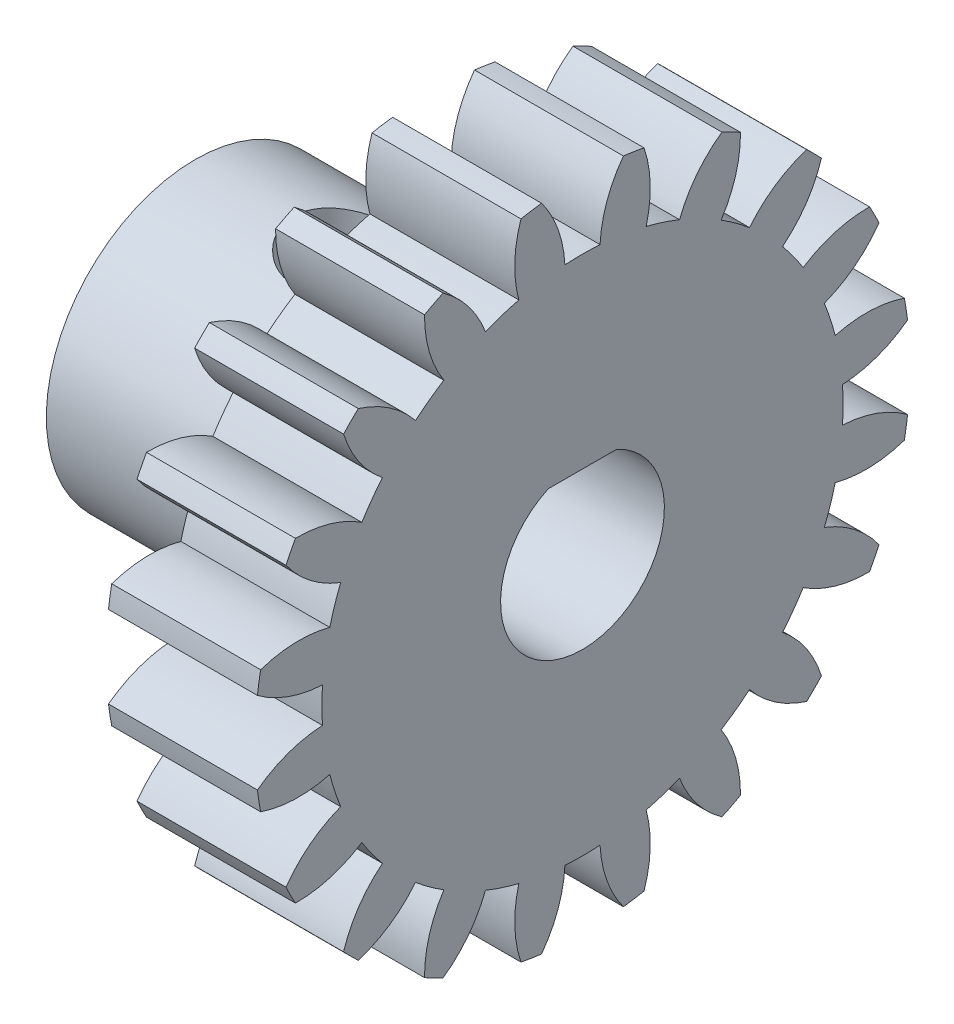
SolidWorks part; units mm, degrees
ref_plane "Plane1" through (0, 0, 0) normal (0, 0, 1) x (1, 0, 0)
ref_plane "Plane2" through (0, 0, 0) normal (0, 1, 0) x (1, 0, 0)
ref_plane "Plane3" through (0, 0, 0) normal (1, 0, 0) x (0, 0, -1)
sketch "HoldingSke" plane through (0, 0, 0) normal (0, 1, 0) x (1, 0, 0)
  line L0 (0, 0) -> (0.9397, -0.342)
  line L1 (-15, 0) -> (100, 0) construction
  line L2 (0, 0) -> (-2.1039, 2.3779)
  line L3 (0, 0) -> (-11.863, 4.5341)
  line L4 (0, 0) -> (8.1152, 2.9537)
  line L5 (0, 0) -> (-14.0543, -5.2418)
  line L6 (0, 0) -> (-4.1448, -2.7965)
  line L7 (-2.1039, 2.3779) -> (1.1249, 17.0263)
  line L8 (-76.2, 54.61) -> (-75.2, 54.61)
  line L9 (-67.7845, 28.3722) -> (-49.3413, 33.142)
  line L10 (-76.2, 71.12) -> (104.1128, 71.12)
  line L11 (0, 0) -> (-5, 0)
  line L12 (-76.2, 101.6) -> (-76.162, 101.6)
  line L13 (24.9733, 27.94) -> (52.9518, 28.4284)
  line L14 (24.9733, 27.94) -> (24.9743, 27.94)
  line L15 (24.9733, 27.94) -> (100.4006, 29.5858)
  line L16 (-63.627, -1) -> (-12.827, -1)
  circle A0 centre (0, 0) radius 3
  circle A1 centre (0, 0) radius 5
  circle A2 centre (0, 0) radius 5
  circle A3 centre (0, 0) radius 3
  dimension "MHD" = 10
  dimension "Hub_dia" = 10
  dimension "Bore" = 6
  dimension "MBD" = 6
  dimension "Num_teeth" = 20
  dimension "Pitch" = 1
  dimension "Overall_len" = 15
  dimension "Show_teeth" = 20
  dimension "Thickness" = 5
  dimension "OAL" = 15.0001
  dimension "T_dim" = 1
  dimension "Ap" = 14.5
  dimension "H" = 19.05
  dimension "Pitch_radius" = 180.3128
  dimension "Width" = 5
  dimension "Backlash" = 0.038
  dimension "Addendum_fac" = 1
  dimension "Dedendum_fac" = 1.25
  dimension "Clearance_fac" = 0.25
  dimension "Dedendum_add" = 0.001
  dimension "Module" = 1
sketch "BasProSke" plane through (0, 0, 0) normal (0, 1, 0) x (1, 0, 0)
  line L0 (-10, 0) -> (60, 0) construction
  line L1 (0, 0) -> (0, 11)
  line L2 (0, 0) -> (5, 0)
  line L3 (5, 0) -> (5, 11)
  line L4 (5, 11) -> (0, 11)
  dimension "Thickness" = 5
  dimension "Diameter" = 22
revolve "Base-Revolve" add sketch "BasProSke" angle 360 about L0
sketch "TooCutSke" plane through (0, 0, 0) normal (1, 0, 0) x (0, 0, -1)
  line L1 (0, 0) -> (0, 107) construction
  line L2 (0, 0) -> (-0.8511, 9.9637) construction
  line L3 (0, 0) -> (-3.1206, 19.7028) construction
  line L4 (-0.8511, 9.9637) -> (-1.5603, 9.8514) construction
  arc A0 (0.5894, 8.7291) -> (-0.5894, 8.7291) centre (0, 0) ccw
  arc A1 (1.3917, 10.9372) -> (-1.3917, 10.9372) centre (0, 0) ccw
  circle A2 centre (0, 0) radius 10 construction
  circle A3 centre (0, 0) radius 9.6815 construction
  arc A4 (-0.5894, 8.7291) -> (-1.3917, 10.9372) centre (-4.5843, 8.5273) ccw
  arc A5 (1.3917, 10.9372) -> (0.5894, 8.7291) centre (4.5843, 8.5273) ccw
  dimension "Root_dia" = 17.498
  dimension "Overcut_dia" = 22.0508
  dimension "Pitch_dia" = 20
  dimension "Base_dia" = 19.363
  dimension "Flank_rad" = 4
  dimension "Half_ang" = 9
  dimension "Half_CT" = 0.7181
extrude "ToothCut" cut sketch "TooCutSke" along normal through all
fillet "Breaks" [suppressed] radius 0.02
fillet "RootFillets" [suppressed] radius 0.251
pattern_circular "TeethCuts" count 20 every 18 about axis through (-10, 0, 0) along (1, 0, 0) of "ToothCut", "RootFillets", "Breaks"
sketch "HubNeaOneSke" plane through (0, 0, 0) normal (-1, 0, 0) x (0, 0, 1)
  circle A0 centre (0, 0) radius 5
  dimension "Diameter" = 10
extrude "HubNearOne" add sketch "HubNeaOneSke" along normal blind 10.0001
sketch "HubNeaBotSke" plane through (0, 0, 0) normal (-1, 0, 0) x (0, 0, 1)
  circle A0 centre (0, 0) radius 5
  dimension "Diameter" = 10
extrude "HubNearBoth" [suppressed] add sketch "HubNeaBotSke" along normal blind 5
ref_plane "FarPln" through (5, 0, 0) normal (1, 0, 0) x (0, 0, -1)
sketch "HubFarSke" plane through (5, 0, 0) normal (1, 0, 0) x (0, 0, -1)
  circle A0 centre (0, 0) radius 5
  dimension "Diameter" = 10
extrude "HubFar" [suppressed] add sketch "HubFarSke" along normal blind 5
sketch "BorSke" plane through (0, 0, 0) normal (1, 0, 0) x (0, 0, -1)
  circle A0 centre (0, 0) radius 3
  dimension "Diameter" = 6
extrude "Bore" cut sketch "BorSke" along normal mid plane 30.0001
sketch "KeySke" plane through (0, 0, 0) normal (1, 0, 0) x (0, 0, -1)
  line L0 (-1, 0) -> (-1, 4)
  line L1 (-1, 4) -> (1, 4)
  line L2 (1, 4) -> (1, 0)
  line L3 (0, 0) -> (0, 34) construction
  line L4 (-1, 0) -> (1, 0)
  dimension "Offset" = 4
  dimension "Width" = 2
extrude "Keyway" [suppressed] cut sketch "KeySke" along normal mid plane 30.0001
pattern_circular "Keyway2" [suppressed] count 2 every 90 about axis through (-10, 0, 0) along (1, 0, 0)
sketch "Sketch2" plane through (0, 0, 0) normal (1, 0, 0) x (0, 0, -1)
  line L0 (-1.65, 2.2) -> (1.65, 2.2)
  circle A0 centre (0, 0) radius 3
  arc A2 (-1.65, 2.2) -> (1.65, 2.2) centre (0, 0) ccw
  dimension "D1" = 2.75
  dimension "D3" = 6
  dimension "D2" = 2.2
extrude "Boss-Extrude1" add sketch "Sketch2" along normal up to surface (15.0001 mm away) from surface at -10.0001 contours L0 A0 up to face at (5, 0, 3) starting at face at (-10.0001, 0, 3)
sketch "Sketch3" plane through (0, 0, 0) normal (0, 1, 0) x (1, 0, 0)
  line L0 (-10.0001, 5) -> (-10.0001, -5) construction
  line L2 (0, 0) -> (-10.0001, 0) construction
  line L3 (0, 5) -> (0, -5) construction
  circle A0 centre (-3.0001, 0) radius 1.7
  dimension "D1" = 3.4
  dimension "D2" = 7
extrude "Cut-Extrude1" cut sketch "Sketch3" along normal blind 10
sketch "Sketch4" plane through (0, 0, 0) normal (0, 0, 1) x (1, 0, 0)
  line L0 (-10.0001, 5) -> (-10.0001, -5) construction
  line L1 (-10.0001, 10.1008) -> (-8.0001, 10.1008)
  line L2 (-10.0001, 10.1008) -> (-10.0001, -10.1008)
  line L3 (-10.0001, -10.1008) -> (-8.0001, -10.1008)
  line L4 (-8.0001, 10.1008) -> (-8.0001, -10.1008)
  line L5 (-10.0001, 10.1008) -> (-8.0001, -10.1008) construction
  line L6 (-10.0001, -10.1008) -> (-8.0001, 10.1008) construction
  point P0 (-9.0001, 0)
  dimension "D1" = 2
  dimension "D2" = 2
extrude "Cut-Extrude2" cut sketch "Sketch4" against normal through all both and the other way through all
sketch "Sketch5" plane through (-8.0001, 0, 0) normal (-1, 0, 0) x (0, 0, 1)
  line L0 (0, 2.75) -> (0, 2.5)
  line L1 (-1.1456, 2.5) -> (1.1456, 2.5)
  circle A0 centre (0, 0) radius 2.75
  point P10 (0, 2.5)
  line M2 (-1.65, 2.2) -> (1.65, 2.2)
  arc M3 (1.65, 2.2) -> (-1.65, 2.2) centre (0, 0) cw
  dimension "D1" = 5.5
  dimension "D2" = 90
extrude "Cut-Extrude3" cut sketch "Sketch5" against normal blind 31 contours L1 A0 M3 M2
equation "' \"Module@HoldingSke\" = 6.35"
equation "' \"Num_teeth@HoldingSke\" = 12"
equation "' \"Ap@HoldingSke\" =  20"
equation "' \"Ap@HoldingSke\" = 20"
equation "' \"Width@HoldingSke\" = 0.5 * 25.4"
equation "' \"Hub_dia@HoldingSke\"= 1 * 25.4"
equation "' \"Hub_dia@HoldingSke\" = 1 * 25.4"
equation "' \"Overall_len@HoldingSke\" = 1.0 * 25.4"
equation "' \"Bore@HoldingSke\" = 0.75 * 25.4"
equation "' \"T_dim@HoldingSke\" = 0.1 * 25.4"
equation "' \"Width@KeySke\" = 0.25 * 25.4"
equation "' \"Show_teeth@HoldingSke\" = 13"
equation "' \"Backlash@HoldingSke\" = 0.009 * 25.4"
equation "' \"Addendum_fac@HoldingSke\" = 1.0"
equation "' \"Dedendum_fac@HoldingSke\" = 1.25"
equation "' \"Dedendum_add@HoldingSke\" = 0.00005 * 25.4"
equation "' \"Clearance_fac@HoldingSke\" = 0.25"
equation "\"Pitch@HoldingSke\" = 1 / \"Module@HoldingSke\""
equation "\"Overcut_dia@TooCutSke\" = (\"Num_teeth@HoldingSke\" + 2 * \"Addendum_fac@HoldingSke\") / \"Pitch@HoldingSke\" + 0.002 * 25.4"
equation "\"Pitch_dia@TooCutSke\" = \"Num_teeth@HoldingSke\" / \"Pitch@HoldingSke\""
equation "\"Base_dia@TooCutSke\" = \"Num_teeth@HoldingSke\" / \"Pitch@HoldingSke\" * cos((\"Ap@HoldingSke\"  * 3.14159265 / 180))"
equation "\"Root_dia@TooCutSke\" = (\"Num_teeth@HoldingSke\" + 2) / \"Pitch@HoldingSke\" - 2 * (\"Addendum_fac@HoldingSke\" + \"Dedendum_fac@HoldingSke\") / \"Pitch@HoldingSke\" - \"Dedendum_add@HoldingSke\" * 2"
equation "\"Half_ang@TooCutSke\" = 180 / \"Num_teeth@HoldingSke\""
equation "\"Half_CT@TooCutSke\" = \"Num_teeth@HoldingSke\" / \"Pitch@HoldingSke\" * sin((3.14159265 / 2 / \"Num_teeth@HoldingSke\")) / 2 - 7 * \"Backlash@HoldingSke\" / 4"
equation "\"Flank_rad@TooCutSke\" = \"Num_teeth@HoldingSke\" / \"Pitch@HoldingSke\" / 5"
equation "\"Radius@RootFillets\" = \"Clearance_fac@HoldingSke\" / \"Pitch@HoldingSke\" + \"Dedendum_add@HoldingSke\""
equation "\"Break_rad@Breaks\" = 0.02 / \"Pitch@HoldingSke\""
equation "\"Thickness@HoldingSke\" = \"Width@HoldingSke\""
equation "\"OAL@HoldingSke\" = \"Thickness@HoldingSke\""
equation "\"MHD@HoldingSke\" = (\"Num_teeth@HoldingSke\" + 2) / \"Pitch@HoldingSke\" - 2 * (\"Addendum_fac@HoldingSke\" + \"Dedendum_fac@HoldingSke\")  / \"Pitch@HoldingSke\" - \"Dedendum_add@HoldingSke\" * 2"
equation "\"MBD@HoldingSke\" = (\"Num_teeth@HoldingSke\" + 2) / \"Pitch@HoldingSke\" - 2 * (\"Addendum_fac@HoldingSke\" + \"Dedendum_fac@HoldingSke\")  / \"Pitch@HoldingSke\" - \"Dedendum_add@HoldingSke\" * 2 - 0.002 * 25.4"
equation "\"MHD@HoldingSke\" = ((sgn( \"MHD@HoldingSke\" - \"Hub_dia@HoldingSke\" )-1)*( \"MHD@HoldingSke\" - \"Hub_dia@HoldingSke\" ))/-2+ \"Hub_dia@HoldingSke\""
equation "\"MBD@HoldingSke\" = ((sgn( \"MBD@HoldingSke\" - \"Bore@HoldingSke\" )-1)*( \"MBD@HoldingSke\" - \"Bore@HoldingSke\" ))/-2+ \"Bore@HoldingSke\""
equation "\"OAL@HoldingSke\" = ((sgn( \"OAL@HoldingSke\" - \"Overall_len@HoldingSke\" )+1)*( \"OAL@HoldingSke\" - \"Overall_len@HoldingSke\" ))/2 + \"Overall_len@HoldingSke\" + 0.000002 * 25.4"
equation "\"Num_teeth@TeethCuts\" = int( \"Show_teeth@HoldingSke\" ) + 1"
equation "\"Num_teeth@TeethCuts\" = ((sgn( \"Num_teeth@TeethCuts\" - \"Num_teeth@HoldingSke\" )-1)*( \"Num_teeth@TeethCuts\" - \"Num_teeth@HoldingSke\" ))/-2+ \"Num_teeth@HoldingSke\""
equation "\"Num_teeth@TeethCuts\" = ((sgn( \"Num_teeth@TeethCuts\" - 2.0)+1)*( \"Num_teeth@TeethCuts\" - 2.0))/2 +2.0"
equation "\"Angle@TeethCuts\" = 360.0 / \"Num_teeth@HoldingSke\""
equation "\"Diameter@BasProSke\" = (\"Num_teeth@HoldingSke\" + 2 * \"Addendum_fac@HoldingSke\") / \"Pitch@HoldingSke\""
equation "\"Thickness@BasProSke\"  = \"Thickness@HoldingSke\""
equation "' \"Fillet_rad@BasProSke\" =  \"Thickness@HoldingSke\" * 0.05"
equation "' \"Fillet_rad@BasProSke\" = \"Thickness@HoldingSke\" * 0.05"
equation "\"MHD@HoldingSke\" = ((sgn( \"MHD@HoldingSke\" - \"Root_dia@TooCutSke\" )-1)*( \"MHD@HoldingSke\" - \"Root_dia@TooCutSke\" ))/-2+ \"Root_dia@TooCutSke\""
equation "\"Diameter@HubNeaOneSke\" = \"MHD@HoldingSke\""
equation "\"Length@HubNearOne\" = \"OAL@HoldingSke\" - \"Thickness@BasProSke\""
equation "\"Diameter@HubNeaBotSke\" = \"MHD@HoldingSke\""
equation "\"Length@HubNearBoth\" = ( \"OAL@HoldingSke\" - \"Thickness@BasProSke\" ) / 2.0"
equation "\"Thickness@FarPln\" = \"Thickness@BasProSke\""
equation "\"Diameter@HubFarSke\" = \"MHD@HoldingSke\""
equation "\"Length@HubFar\" = ( \"OAL@HoldingSke\" - \"Thickness@BasProSke\" ) / 2.0"
equation "\"Diameter@BorSke\" = \"MBD@HoldingSke\""
equation "\"D1@Bore\" = \"OAL@HoldingSke\" * 2.0"
equation "\"D1@Keyway\" = \"OAL@HoldingSke\" * 2.0"
equation "\"Offset@KeySke\" = \"T_dim@HoldingSke\" + \"MBD@HoldingSke\" / 2.0"
